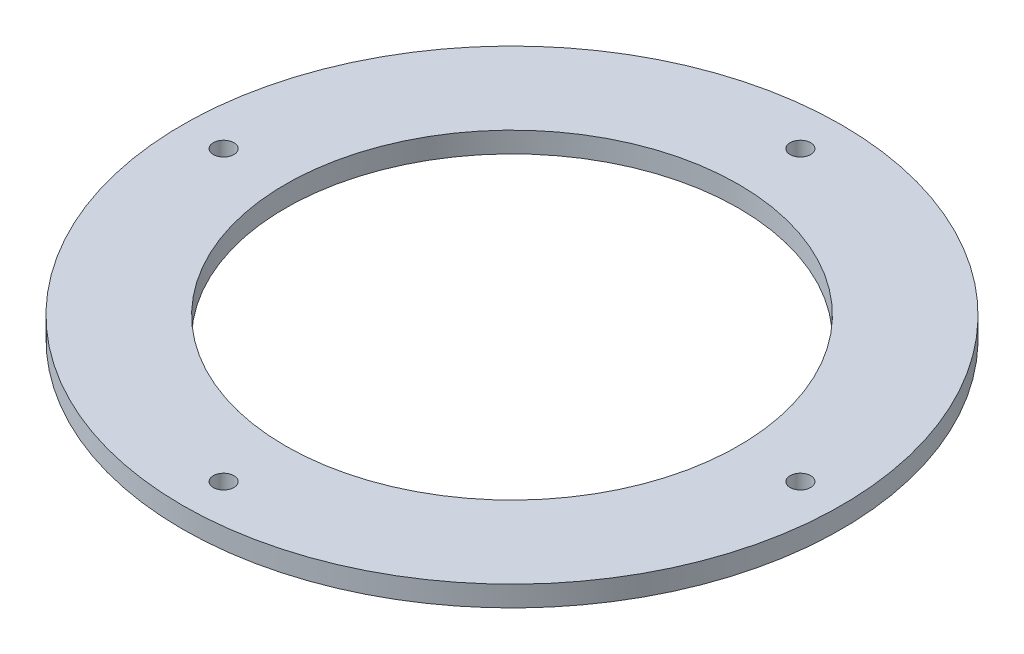
SolidWorks part; units mm, degrees
material "Wrought Stainless Steel"
ref_plane "Front Plane" through (0, 0, 0) normal (0, 0, 1) x (1, 0, 0)
ref_plane "Top Plane" through (0, 0, 0) normal (0, 1, 0) x (1, 0, 0)
ref_plane "Right Plane" through (0, 0, 0) normal (1, 0, 0) x (0, 0, -1)
sketch "Sketch1" plane through (0, 0, 0) normal (0, 1, 0) x (1, 0, 0)
  circle A0 centre (0, 0) radius 69.85
  circle A1 centre (0, 0) radius 101.6
  dimension "D1" = 139.7
  dimension "D2" = 203.2
extrude "Boss-Extrude1" add sketch "Sketch1" along normal blind 6.35
sketch "Sketch2" plane through (0, 6.35, 0) normal (0, 1, 0) x (1, 0, 0)
  circle A0 centre (0, 88.9) radius 3.175
  circle A1 centre (88.9, 0) radius 3.175
  circle A2 centre (0, -88.9) radius 3.175
  circle A3 centre (-88.9, 0) radius 3.175
  circle A4 centre (0, 0) radius 101.6 construction
  dimension "D1" = 88.9
  dimension "D2" = 6.35
  dimension "D3" = 88.9
  dimension "D4" = 88.9
  dimension "D5" = 88.9
extrude "Cut-Extrude1" cut sketch "Sketch2" against normal blind 6.35
